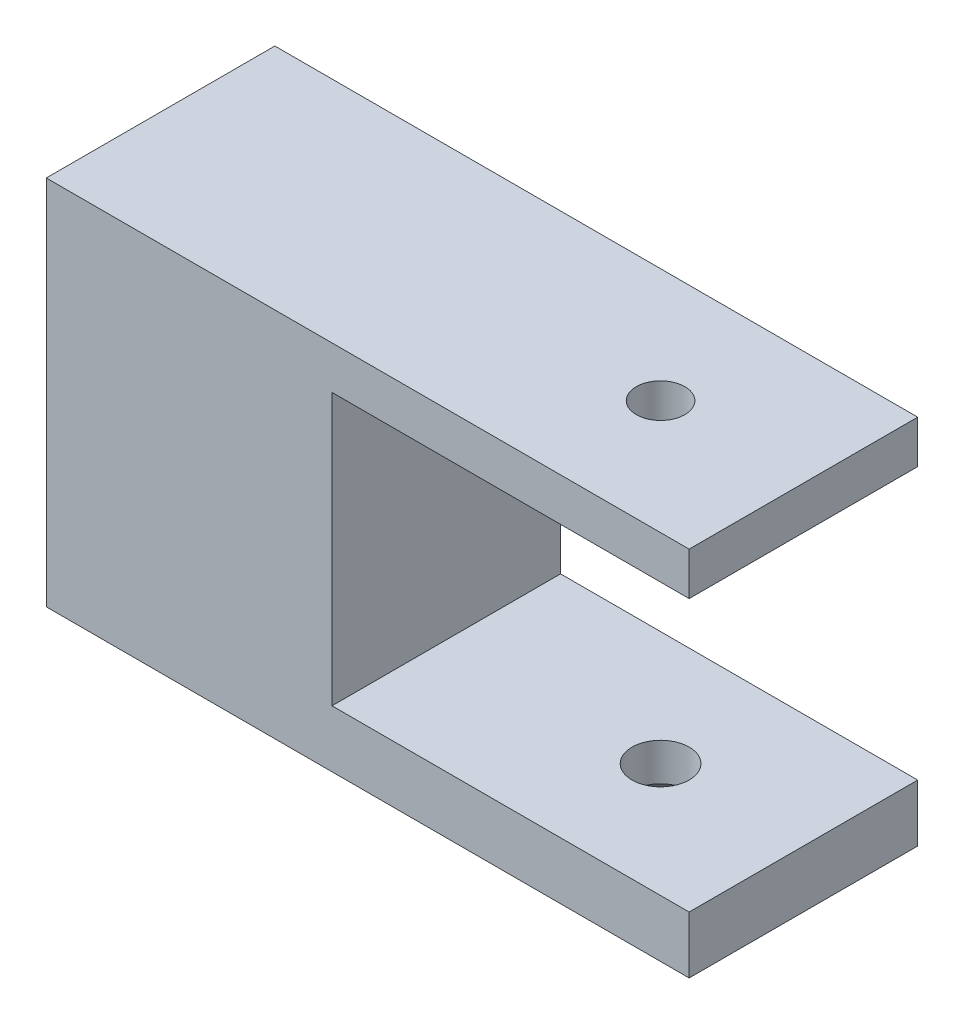
SolidWorks part; units mm, degrees
ref_plane "Alzado" through (0, 0, 0) normal (0, 0, 1) x (1, 0, 0)
ref_plane "Planta" through (0, 0, 0) normal (0, 1, 0) x (1, 0, 0)
ref_plane "Vista lateral" through (0, 0, 0) normal (1, 0, 0) x (0, 0, -1)
sketch "Croquis1" plane through (0, 0, 0) normal (0, 0, 1) x (1, 0, 0)
  line L0 (-121.7854, 32.44) -> (-153.7854, 32.44)
  line L1 (-121.7854, 32.44) -> (-121.7854, 29.44)
  line L2 (-121.7854, 29.44) -> (-146.7854, 29.44)
  line L3 (-146.7854, 29.44) -> (-146.7854, 10.44)
  line L4 (-146.7854, 10.44) -> (-121.7854, 10.44)
  line L5 (-121.7854, 10.44) -> (-121.7854, 6.44)
  line L6 (-121.7854, 6.44) -> (-166.7854, 6.44)
  line L7 (-166.7854, 6.44) -> (-166.7854, 32.44)
  line L8 (-166.7854, 32.44) -> (-153.7854, 32.44)
  dimension "D1" = 25
  dimension "D2" = 19
  dimension "D3" = 20
extrude "Saliente-Extruir1" add sketch "Croquis1" along normal blind 16
sketch "Croquis2" plane through (-166.7854, 0, 0) normal (-1, 0, 0) x (0, 0, 1)
  line L0 (0, 6.44) -> (16, 32.44) construction
  circle A0 centre (8, 19.44) radius 6.2
extrude "Cortar-Extruir1" cut sketch "Croquis2" against normal blind 17
sketch "Croquis3" plane through (0, 6.44, 0) normal (0, -1, 0) x (1, 0, 0)
  line L0 (-166.7854, 0) -> (-121.7854, 0) construction
  line L1 (-121.7854, 16) -> (-121.7854, 0) construction
  circle A0 centre (-131.7854, 8) radius 2
  dimension "D1" = 8
  dimension "D2" = 10
extrude "Cortar-Extruir2" cut sketch "Croquis3" against normal up to vertex (4 mm away)
hole_wizard "Refrentado para tornillo tapón con cabeza plana de clavija de M31" positions "Croquis5" profile "Croquis4" countersink size "M3" standard "Ansi Metric" end condition through all
sketch "Croquis5" plane through (0, 6.44, 0) normal (0, -1, 0) x (-1, 0, 0)
  point P0 (131.7854, -8)
sketch "Croquis4" plane through (-131.7854, 6.44, 8) normal (1, 0, 0) x (0, 0, -1)
  line L0 (0, 0) -> (0, 26)
  line L1 (0, 26) -> (1.7, 26)
  line L2 (1.7, 26) -> (1.7, 1.66)
  line L3 (1.7, 1.66) -> (3.36, 0)
  line L5 (3.36, 0) -> (0, 0)
  line L6 (-1.7, 1.66) -> (-3.36, 0) construction
  line L11 (0, -6.35) -> (0, 107.95) construction
  dimension "Diámetro de taladro hasta el siguiente" = 3.4
  dimension "Profundidad de taladro hasta el siguiente" = 26
  dimension "Diámetro de avellanado cercano" = 6.72
  dimension "Ángulo de avellanado cercano" = 90
sketch "Croquis6" plane through (0, 0, 0) normal (0, 0, -1) x (-1, 0, 0)
  line L0 (166.7854, 19.44) -> (146.7854, 19.44) construction
  line L1 (166.7854, 32.44) -> (166.7854, 6.44) construction
  line L2 (146.7854, 10.44) -> (146.7854, 29.44) construction
  circle A0 centre (152.7854, 19.44) radius 3.5
  dimension "D1" = 14
extrude "Cortar-Extruir3" cut sketch "Croquis6" against normal blind 10
